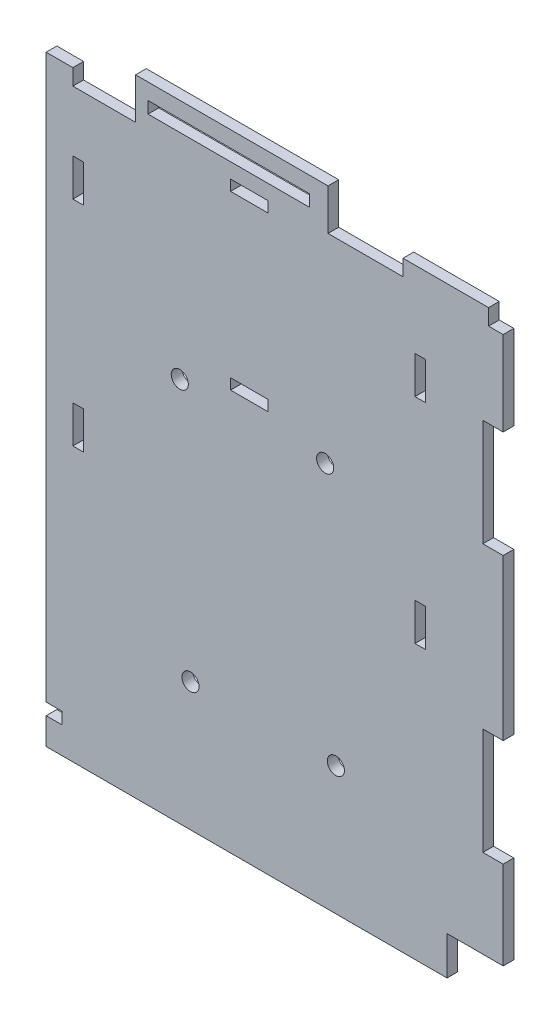
SolidWorks part; units mm, degrees
ref_plane "Ebene vorne" through (0, 0, 0) normal (0, 0, 1) x (1, 0, 0)
ref_plane "Ebene oben" through (0, 0, 0) normal (0, 1, 0) x (1, 0, 0)
ref_plane "Ebene rechts" through (0, 0, 0) normal (1, 0, 0) x (0, 0, -1)
sketch "Skizze1" plane through (0, 0, 0) normal (0, 0, 1) x (1, 0, 0)
  line L0 (39.2787, -130.5311) -> (-35.7213, -130.5311)
  line L1 (-35.7213, -130.5311) -> (-35.7213, -125.5311)
  line L2 (-35.7213, -125.5311) -> (-32.7213, -125.5311)
  line L3 (-32.7213, -125.5311) -> (-32.7213, -123.3311)
  line L4 (-32.7213, -123.3311) -> (-35.7213, -123.3311)
  line L5 (-35.7213, -123.3311) -> (-35.7213, -18.0311)
  line L6 (-35.7213, -18.0311) -> (-30.7213, -18.0311)
  line L7 (-30.7213, -18.0311) -> (-30.7213, -21.0311)
  line L8 (-30.7213, -21.0311) -> (-28.6895, -21.0311)
  line L12 (-23.4281, -21.0311) -> (-18.9904, -21.0311)
  line L13 (-18.9904, -21.0311) -> (-18.9904, -13.3311)
  line L14 (-18.9904, -13.3311) -> (17.0096, -13.3311)
  line L15 (17.0096, -13.3311) -> (17.0096, -21.0311)
  line L16 (17.0096, -21.0311) -> (22.5009, -21.0311)
  line L20 (28.5009, -21.0311) -> (31.0457, -21.0311)
  line L21 (31.0457, -21.0311) -> (31.0457, -18.0311)
  line L22 (31.0457, -18.0311) -> (47.0457, -18.0311)
  line L23 (47.0457, -18.0311) -> (47.0457, -21.0311)
  line L24 (47.0457, -21.0311) -> (49.7787, -21.0311)
  line L25 (49.7787, -21.0311) -> (49.7787, -36.8311)
  line L26 (49.7787, -36.8311) -> (45.9787, -36.8311)
  line L27 (45.9787, -36.8311) -> (45.9787, -56.8311)
  line L28 (45.9787, -56.8311) -> (49.7787, -56.8311)
  line L29 (49.7787, -56.8311) -> (49.7787, -86.8311)
  line L30 (49.7787, -86.8311) -> (45.9787, -86.8311)
  line L31 (45.9787, -86.8311) -> (45.9787, -106.8311)
  line L32 (45.9787, -106.8311) -> (49.7787, -106.8311)
  line L33 (49.7787, -106.8311) -> (49.7787, -123.3311)
  line L34 (49.7787, -123.3311) -> (39.2787, -123.3311)
  line L35 (39.2787, -123.3311) -> (39.2787, -130.5311)
  line L36 (-28.6895, -21.0311) -> (-23.4281, -21.0311)
  line L37 (22.5009, -21.0311) -> (28.5009, -21.0311)
  point P11 (28.5009, -21.0311)
  dimension "D2" = 5
  dimension "D3" = 3
  dimension "D4" = 2.2
  dimension "D5" = 3
  dimension "D6" = 102.3
  dimension "D7" = 5
  dimension "D8" = 3
  dimension "D9" = 11.7309
  dimension "D10" = 36
  dimension "D11" = 14.0361
  dimension "D12" = 2.0317
  dimension "D13" = 4.4378
  dimension "D16" = 75
  dimension "D17" = 16
  dimension "D18" = 16.5
  dimension "D19" = 3.8
  dimension "D21" = 20
  dimension "D22" = 30
  dimension "D23" = 20
  dimension "D26" = 10.5
  dimension "D27" = 18.0311
  dimension "D28" = 47.0457
  dimension "D29" = 13.3311
extrude "Aufsatz-Linear austragen1" add sketch "Skizze1" along normal blind 2
sketch "Skizze2" plane through (0, 0, 2) normal (0, 0, 1) x (1, 0, 0)
  line L0 (-10.7213, -58.5311) -> (16.4787, -58.5311) construction
  line L1 (-35.7213, -130.5311) -> (39.2787, -130.5311) construction
  line L2 (-35.7213, -123.3311) -> (-32.7213, -123.3311) construction
  line L3 (-30.7213, -32.3311) -> (-28.7213, -32.3311)
  line L4 (-30.7213, -32.3311) -> (-30.7213, -39.3311)
  line L5 (-30.7213, -39.3311) -> (-28.7213, -39.3311)
  line L6 (-28.7213, -32.3311) -> (-28.7213, -39.3311)
  line L7 (33.2787, -32.3311) -> (35.2787, -32.3311)
  line L8 (33.2787, -32.3311) -> (33.2787, -39.3311)
  line L9 (33.2787, -39.3311) -> (35.2787, -39.3311)
  line L10 (35.2787, -32.3311) -> (35.2787, -39.3311)
  line L11 (-30.7213, -72.3311) -> (-28.7213, -72.3311)
  line L12 (-30.7213, -72.3311) -> (-30.7213, -79.3311)
  line L13 (-30.7213, -79.3311) -> (-28.7213, -79.3311)
  line L14 (-28.7213, -72.3311) -> (-28.7213, -79.3311)
  line L15 (33.2787, -72.3311) -> (35.2787, -72.3311)
  line L16 (33.2787, -72.3311) -> (33.2787, -79.3311)
  line L17 (33.2787, -79.3311) -> (35.2787, -79.3311)
  line L18 (35.2787, -72.3311) -> (35.2787, -79.3311)
  line L19 (-35.7213, -18.0311) -> (-35.7213, -123.3311) construction
  line L20 (17.0096, -13.3311) -> (-18.9904, -13.3311) construction
  line L21 (-1.2213, -53.5311) -> (5.7787, -53.5311)
  line L22 (-1.2213, -53.5311) -> (-1.2213, -55.5311)
  line L23 (-1.2213, -55.5311) -> (5.7787, -55.5311)
  line L24 (5.7787, -53.5311) -> (5.7787, -55.5311)
  line L25 (-1.2213, -21.3311) -> (5.7787, -21.3311)
  line L26 (-1.2213, -21.3311) -> (-1.2213, -23.3311)
  line L27 (-1.2213, -23.3311) -> (5.7787, -23.3311)
  line L28 (5.7787, -21.3311) -> (5.7787, -23.3311)
  circle A0 centre (-10.7213, -58.5311) radius 1.6
  circle A1 centre (16.4787, -58.5311) radius 1.6
  circle A2 centre (-8.7213, -106.5311) radius 1.6
  circle A3 centre (18.4787, -106.5311) radius 1.6
  dimension "D1" = 3.2
  dimension "D2" = 3.2
  dimension "D3" = 3.2
  dimension "D4" = 3.2
  dimension "D5" = 27.2
  dimension "D6" = 48
  dimension "D7" = 2
  dimension "D8" = 27.2
  dimension "D9" = 48
  dimension "D10" = 7
  dimension "D11" = 2
  dimension "D12" = 7
  dimension "D13" = 2
  dimension "D14" = 62
  dimension "D15" = 33
  dimension "D16" = 44
  dimension "D17" = 5
  dimension "D18" = 72
  dimension "D19" = 25
  dimension "D20" = 2
  dimension "D21" = 7
  dimension "D22" = 27.5
  dimension "D23" = 30.2
  dimension "D24" = 2
  dimension "D25" = 8
extrude "Schnitt-Linear austragen1" cut sketch "Skizze2" against normal up to surface (2 mm away) up to face at (15.8427, -64.4669, 0)
sketch "Skizze3" plane through (0, 0, 2) normal (0, 0, 1) x (1, 0, 0)
  line L0 (-18.9904, -21.0311) -> (-30.7213, -21.0311) construction
  line L1 (-16.6618, -16.3311) -> (13.5382, -16.3311)
  line L2 (-16.6618, -16.3311) -> (-16.6618, -18.5311)
  line L3 (-16.6618, -18.5311) -> (13.5382, -18.5311)
  line L4 (13.5382, -16.3311) -> (13.5382, -18.5311)
  line L5 (-18.9904, -13.3311) -> (-18.9904, -21.0311) construction
  dimension "D1" = 30.2
  dimension "D2" = 2.2
  dimension "D3" = 2.5
  dimension "D4" = 2.3285
extrude "Schnitt-Linear austragen2" cut sketch "Skizze3" against normal up to surface (2 mm away) up to face at (34.2787, -35.8311, 0)
